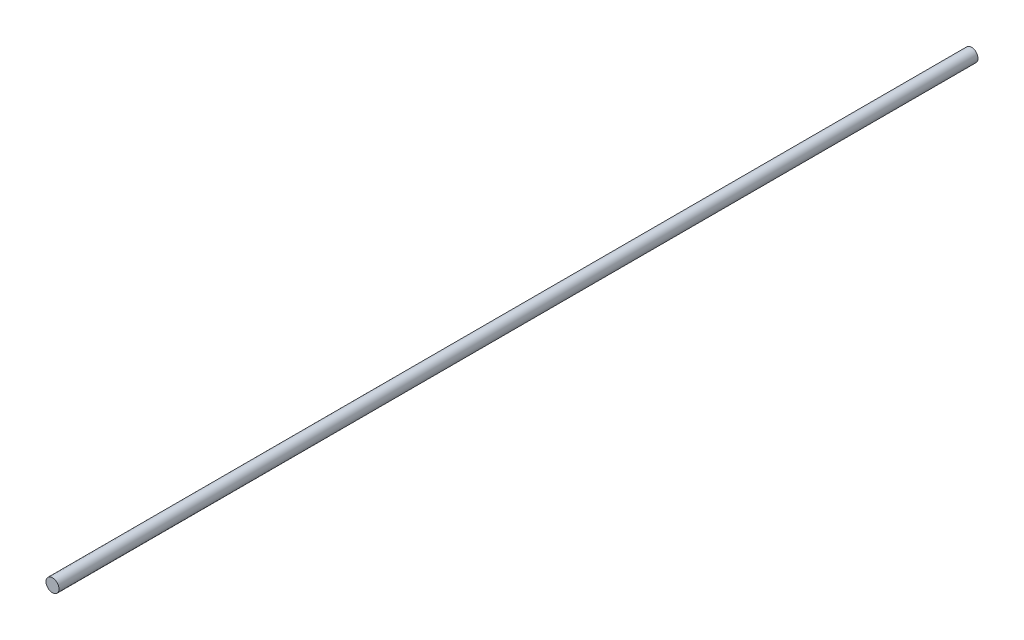
SolidWorks part; units mm, degrees
ref_plane "Plan de face" through (0, 0, 0) normal (0, 0, 1) x (1, 0, 0)
ref_plane "Plan de dessus" through (0, 0, 0) normal (0, 1, 0) x (1, 0, 0)
ref_plane "Plan de droite" through (0, 0, 0) normal (1, 0, 0) x (0, 0, -1)
sketch "Esquisse1" plane through (0, 0, 0) normal (0, 0, 1) x (1, 0, 0)
  circle A0 centre (0, 0) radius 4
  dimension "D1" = 8
extrude "Boss.-Extru.1" add sketch "Esquisse1" along normal blind 565
